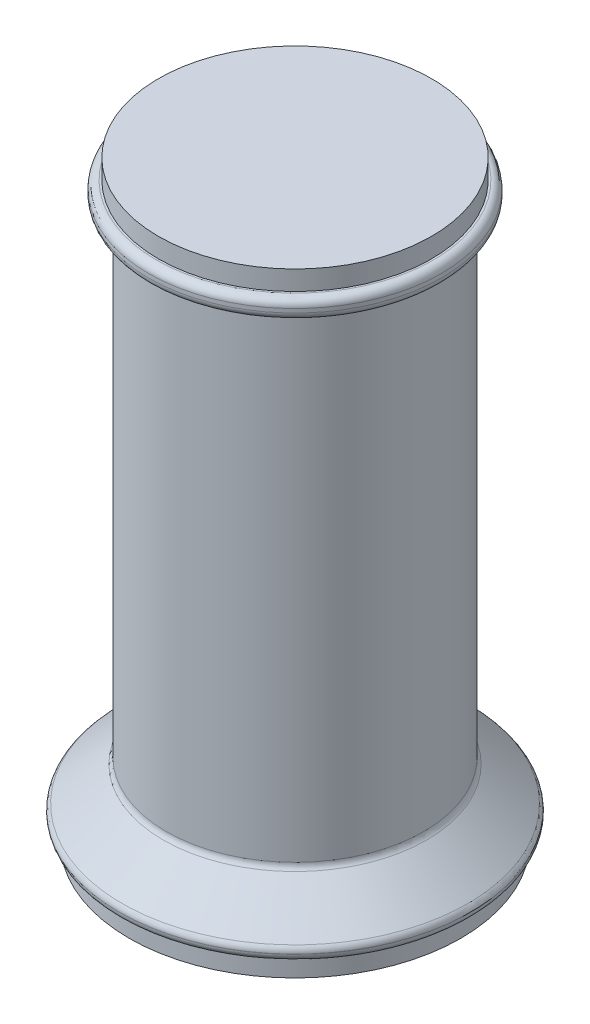
SolidWorks part; units mm, degrees
material "1060 Alloy"
ref_plane "Front Plane" through (0, 0, 0) normal (0, 0, 1) x (1, 0, 0)
ref_plane "Top Plane" through (0, 0, 0) normal (0, 1, 0) x (1, 0, 0)
ref_plane "Right Plane" through (0, 0, 0) normal (1, 0, 0) x (0, 0, -1)
sketch "Sketch1" plane through (0, 0, 0) normal (0, 1, 0) x (1, 0, 0)
  circle A0 centre (0, 0) radius 42.5
  dimension "D1" = 85
extrude "Boss-Extrude1" add sketch "Sketch1" along normal blind 5
sketch "Sketch2" plane through (0, 5, 0) normal (0, 1, 0) x (1, 0, 0)
  circle A0 centre (0, 0) radius 45
  dimension "D1" = 90
extrude "Boss-Extrude2" add sketch "Sketch2" along normal blind 3
ref_plane "Plane1" through (0, 18, 0) normal (0, 1, 0) x (1, 0, 0)
sketch "Sketch3" plane through (0, 18, 0) normal (0, 1, 0) x (1, 0, 0)
  circle A0 centre (0, 0) radius 33
  dimension "D1" = 66
loft "Loft1" add profiles "Sketch3" section face at (0, 8, 45) section "Sketch3"
sketch "Sketch4" plane through (0, 18, 0) normal (0, 1, 0) x (1, 0, 0)
  circle A1 centre (0, 0) radius 33
  circle A2 centre (0, 0) radius 33
  dimension "D1" = 0
extrude "Boss-Extrude3" add sketch "Sketch4" along normal blind 142 from surface at -18 starting at face at (0, 0, 42.5)
sketch "Sketch5" plane through (0, 142, 0) normal (0, 1, 0) x (1, 0, 0)
  circle A0 centre (0, 0) radius 37.5
  dimension "D1" = 75
extrude "Boss-Extrude4" add sketch "Sketch5" along normal blind 5 contours A0
fillet "Fillet1" radius 2 4 edges at (0, 5, 45) (0, 8, 45) (0, 142, 33) (0, 18, 33)
fillet "Fillet2" radius 2 2 edges at (0, 142, 37.5) (0, 147, 37.5)
sketch "Sketch7" plane through (0, 147, 0) normal (0, 1, 0) x (1, 0, 0)
  circle A0 centre (0, 0) radius 35
  dimension "D1" = 70
extrude "Boss-Extrude5" add sketch "Sketch7" along normal blind 5
